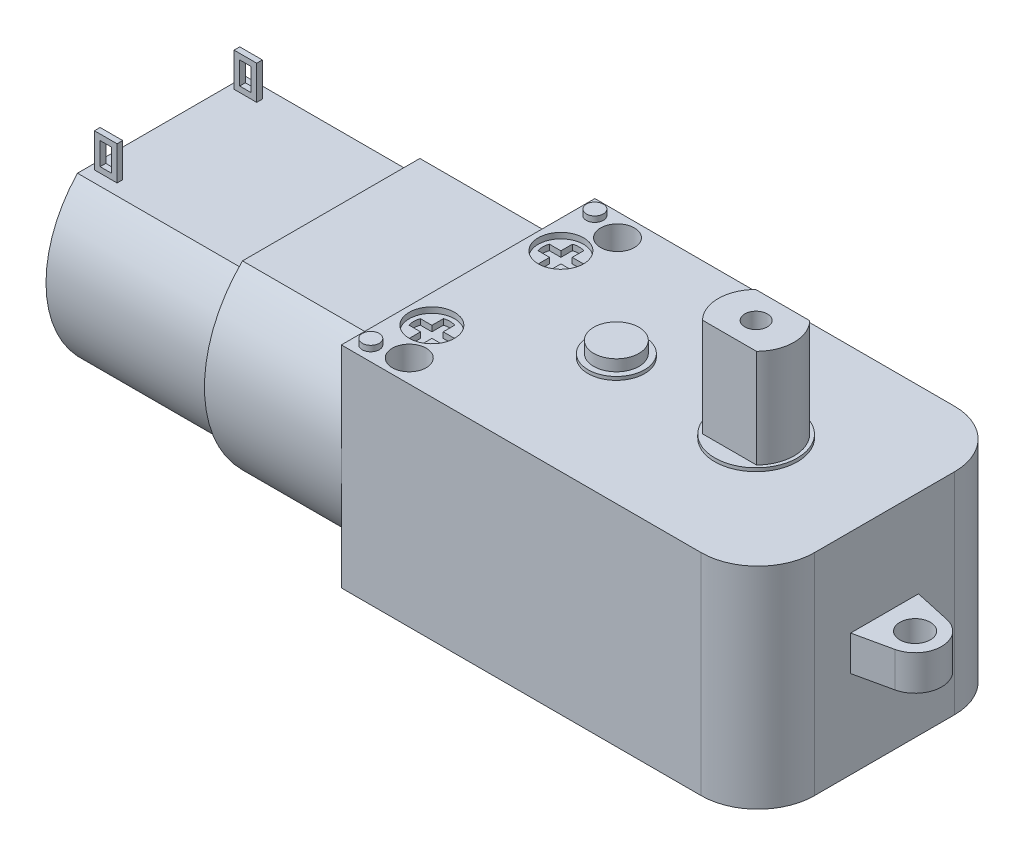
SolidWorks part; units mm, degrees
ref_plane "Front Plane" through (0, 0, 0) normal (0, 0, 1) x (1, 0, 0)
ref_plane "Top Plane" through (0, 0, 0) normal (0, 1, 0) x (1, 0, 0)
ref_plane "Right Plane" through (0, 0, 0) normal (1, 0, 0) x (0, 0, -1)
sketch "Sketch1" plane through (0, 0, 0) normal (0, 1, 0) x (1, 0, 0)
  line L1 (0, 0) -> (36.8, 0)
  line L2 (0, 0) -> (0, 22.4)
  line L3 (0, 22.4) -> (36.8, 22.4)
  line L4 (36.8, 0) -> (36.8, 22.4)
  dimension "D1" = 36.8
  dimension "D2" = 22.4
extrude "Extrude1" add sketch "Sketch1" along normal mid plane 18.6
fillet "Fillet1" radius 5 2 edges at (36.8, 0, -22.4) (36.8, 0, 0)
sketch "Sketch2" plane through (0, 0, 0) normal (0, 1, 0) x (1, 0, 0)
  line L0 (36.8, 11.2) -> (43.7927, 11.2) construction
  line L1 (36.8, 5) -> (36.8, 17.4) construction
  line L2 (36.8, 14.2) -> (40.0048, 13.4951)
  line L3 (36.8, 8.2) -> (40.0048, 8.9049)
  line L4 (36.8, 14.2) -> (36.8, 8.2)
  circle A0 centre (39.5, 11.2) radius 1.35
  arc A1 (40.0048, 8.9049) -> (40.0048, 13.4951) centre (39.5, 11.2) ccw
  dimension "D1" = 2.7
  dimension "D3" = 1
  dimension "D2" = 3
  dimension "D4" = 2.7
extrude "Extrude2" add sketch "Sketch2" along normal mid plane 3.1
sketch "Sketch3" plane through (0, 9.3, 0) normal (0, 1, 0) x (1, 0, 0)
  line L0 (36.8, 11.2) -> (0, 11.2) construction
  line L1 (36.8, 5) -> (36.8, 17.4) construction
  line L2 (0, 22.4) -> (0, 0) construction
  circle A0 centre (25.45, 11.2) radius 3.65
  circle A1 centre (13.1, 11.2) radius 2.5
  dimension "D1" = 7.3
  dimension "D2" = 11.35
  dimension "D3" = 5
  dimension "D4" = 12.35
extrude "Extrude3" add sketch "Sketch3" along normal blind 0.3
sketch "Sketch4" plane through (0, 9.6, 0) normal (0, 1, 0) x (1, 0, 0)
  line L0 (22.1, 11.2) -> (28.8, 11.2) construction
  line L1 (23.0625, 8.85) -> (27.8375, 8.85)
  line L2 (23.0625, 13.55) -> (27.8375, 13.55)
  line L3 (22.1, 13.55) -> (28.8, 13.55) construction
  line L4 (22.1, 8.85) -> (28.8, 8.85) construction
  arc A0 (23.0625, 13.55) -> (23.0625, 8.85) centre (25.45, 11.2) ccw
  circle A1 centre (25.45, 11.2) radius 1
  arc A2 (27.8375, 8.85) -> (27.8375, 13.55) centre (25.45, 11.2) ccw
  dimension "D1" = 6.7
  dimension "D2" = 2
  dimension "D3" = 2.35
  dimension "D4" = 2.35
extrude "Extrude4" add sketch "Sketch4" along normal blind 8.7
sketch "Sketch6" plane through (0, 9.6, 0) normal (0, 1, 0) x (1, 0, 0)
  circle A0 centre (13.1, 11.2) radius 2
  dimension "D1" = 4
extrude "Extrude5" add sketch "Sketch6" along normal blind 1
sketch "Sketch7" plane through (0, 9.3, 0) normal (0, 1, 0) x (1, 0, 0)
  line L0 (4, 22.4) -> (4, 0) construction
  line L1 (31.8, 22.4) -> (0, 22.4) construction
  line L2 (0, 0) -> (31.8, 0) construction
  line L3 (0, 22.4) -> (0, 0) construction
  circle A0 centre (4, 20.4) radius 1.5
  circle A1 centre (4, 2) radius 1.5
  dimension "D1" = 3
  dimension "D2" = 2
  dimension "D3" = 2
  dimension "D4" = 4
extrude "Extrude6" cut sketch "Sketch7" against normal through all
sketch "Sketch8" plane through (0, 9.3, 0) normal (0, 1, 0) x (1, 0, 0)
  line L0 (2.5, 22.4) -> (2.5, 0) construction
  line L1 (31.8, 22.4) -> (0, 22.4) construction
  line L2 (0, 0) -> (31.8, 0) construction
  line L3 (0, 22.4) -> (0, 0) construction
  circle A0 centre (2.5, 16.9) radius 2
  circle A1 centre (2.5, 5.5) radius 2
  dimension "D1" = 4
  dimension "D2" = 5.5
  dimension "D3" = 5.5
  dimension "D4" = 2.5
extrude "Extrude7" cut sketch "Sketch8" against normal blind 0.5
sketch "Sketch9" plane through (0, 8.8, 0) normal (0, 1, 0) x (1, 0, 0)
  line L0 (2.5, 18.5) -> (2.5, 15.3) construction
  line L1 (4.1, 16.9) -> (0.9, 16.9) construction
  line L2 (0.9, 5.5) -> (4.1, 5.5) construction
  line L3 (2.5, 7.1) -> (2.5, 3.9) construction
  line L4 (2, 7.0199) -> (2, 6)
  line L5 (3, 7.0199) -> (3, 6)
  line L6 (4.0199, 17.4) -> (3, 17.4)
  line L7 (2, 18.4199) -> (2, 17.4)
  line L8 (0.9801, 5) -> (2, 5)
  line L9 (4.0199, 16.4) -> (3, 16.4)
  line L10 (3, 18.4199) -> (3, 17.4)
  line L11 (0.9801, 6) -> (2, 6)
  line L12 (2, 18.5) -> (2, 15.3) construction
  line L13 (3, 18.5) -> (3, 15.3) construction
  line L14 (4.1, 17.4) -> (0.9, 17.4) construction
  line L15 (4.1, 16.4) -> (0.9, 16.4) construction
  line L16 (2, 7.1) -> (2, 3.9) construction
  line L17 (3, 7.1) -> (3, 3.9) construction
  line L18 (0.9, 6) -> (4.1, 6) construction
  line L19 (0.9, 5) -> (4.1, 5) construction
  line L20 (2, 17.4) -> (0.9801, 17.4)
  line L21 (2, 16.4) -> (2, 15.3801)
  line L22 (3, 16.4) -> (3, 15.3801)
  line L23 (2, 16.4) -> (0.9801, 16.4)
  line L24 (3, 6) -> (4.0199, 6)
  line L25 (2, 5) -> (2, 3.9801)
  line L26 (3, 5) -> (3, 3.9801)
  line L27 (3, 5) -> (4.0199, 5)
  arc A0 (3, 7.0199) -> (2, 7.0199) centre (2.5, 5.5) ccw
  arc A1 (3, 18.4199) -> (2, 18.4199) centre (2.5, 16.9) ccw
  arc A2 (4.0199, 16.4) -> (4.0199, 17.4) centre (2.5, 16.9) ccw
  arc A3 (2, 15.3801) -> (3, 15.3801) centre (2.5, 16.9) ccw
  arc A4 (0.9801, 17.4) -> (0.9801, 16.4) centre (2.5, 16.9) ccw
  arc A5 (4.0199, 5) -> (4.0199, 6) centre (2.5, 5.5) ccw
  arc A6 (2, 3.9801) -> (3, 3.9801) centre (2.5, 5.5) ccw
  arc A7 (0.9801, 6) -> (0.9801, 5) centre (2.5, 5.5) ccw
  dimension "D1" = 3.2
  dimension "D6" = 1.6
  dimension "D2" = 0.5
  dimension "D3" = 0.5
  dimension "D4" = 0.5
  dimension "D5" = 0.5
extrude "Extrude8" cut sketch "Sketch9" against normal blind 0.5
sketch "Sketch10" plane through (0, 9.3, 0) normal (0, 1, 0) x (1, 0, 0)
  line L0 (1.3, 22.4) -> (1.3, 0) construction
  line L1 (31.8, 22.4) -> (0, 22.4) construction
  line L2 (0, 0) -> (31.8, 0) construction
  line L3 (0, 22.4) -> (0, 0) construction
  circle A0 centre (1.3, 21.1) radius 0.75
  circle A1 centre (1.3, 1.3) radius 0.75
  dimension "D1" = 1.5
  dimension "D3" = 1.3
  dimension "D4" = 1.3
  dimension "D2" = 1.3
extrude "Extrude9" add sketch "Sketch10" along normal blind 0.5
sketch "Sketch12" plane through (0, 0, 0) normal (-1, 0, 0) x (0, 0, 1)
  line L0 (-22.4, 9.3) -> (0, -9.3) construction
  line L1 (-19.0384, 8) -> (-3.3616, 8)
  line L4 (-3.3616, -8) -> (-19.0384, -8)
  line L5 (-11.2, 0) -> (-22.4, 0) construction
  arc A0 (-19.0384, 8) -> (-19.0384, -8) centre (-11.2, 0) ccw
  arc A1 (-3.3616, -8) -> (-3.3616, 8) centre (-11.2, 0) ccw
  dimension "D1" = 16
  dimension "D2" = 8
extrude "Extrude11" add sketch "Sketch12" along normal blind 12.1
sketch "Sketch13" plane through (-12.1, 0, 0) normal (-1, 0, 0) x (0, 0, 1)
  line L14 (-18.6189, -7) -> (-3.7811, -7)
  line L15 (-3.7811, 7) -> (-18.6189, 7)
  line L16 (-18.6189, -7) -> (-3.7811, -7)
  line L17 (-3.7811, 7) -> (-18.6189, 7)
  arc A14 (-18.6189, 7) -> (-18.6189, -7) centre (-11.2, 0) ccw
  arc A15 (-3.7811, -7) -> (-3.7811, 7) centre (-11.2, 0) ccw
  arc A16 (-18.6189, 7) -> (-18.6189, -7) centre (-11.2, 0) ccw
  arc A17 (-3.7811, -7) -> (-3.7811, 7) centre (-11.2, 0) ccw
  dimension "D3" = 1
extrude "Extrude12" add sketch "Sketch13" along normal blind 15
sketch "Sketch14" plane through (-27.1, 0, 0) normal (-1, 0, 0) x (0, 0, 1)
  line L0 (-18.6189, -7) -> (-3.7811, 7) construction
  circle A0 centre (-11.2, 0) radius 4
  dimension "D1" = 8
extrude "Extrude13" add sketch "Sketch14" along normal blind 1
sketch "Sketch15" plane through (-28.1, 0, 0) normal (-1, 0, 0) x (0, 0, 1)
  circle A0 centre (-11.2, 0) radius 1
  dimension "D1" = 2
extrude "Extrude14" add sketch "Sketch15" along normal blind 1
sketch "Sketch16" plane through (0, 7, 0) normal (0, 1, 0) x (1, 0, 0)
  line L0 (-27.1, 18.6189) -> (-12.1, 18.6189) construction
  line L1 (-26.6, 17.6189) -> (-24.6, 17.6189)
  line L2 (-26.6, 17.6189) -> (-26.6, 17.1189)
  line L3 (-26.6, 17.1189) -> (-24.6, 17.1189)
  line L4 (-24.6, 17.6189) -> (-24.6, 17.1189)
  line L5 (-26.6, 5.2811) -> (-24.6, 5.2811)
  line L6 (-26.6, 5.2811) -> (-26.6, 4.7811)
  line L7 (-26.6, 4.7811) -> (-24.6, 4.7811)
  line L8 (-24.6, 5.2811) -> (-24.6, 4.7811)
  line L9 (-27.1, 3.7811) -> (-12.1, 3.7811) construction
  line L10 (-27.1, 3.7811) -> (-27.1, 18.6189) construction
  dimension "D1" = 2
  dimension "D2" = 0.5
  dimension "D3" = 0.5
  dimension "D4" = 2
  dimension "D5" = 1
  dimension "D6" = 1
  dimension "D7" = 0.5
  dimension "D8" = 0.5
extrude "Extrude15" add sketch "Sketch16" along normal blind 3
sketch "Sketch17" plane through (0, 0, -4.7811) normal (0, 0, 1) x (1, 0, 0)
  line L0 (-26.6, 10) -> (-24.6, 10) construction
  line L1 (-26.1, 9.5) -> (-25.1, 9.5)
  line L2 (-26.1, 9.5) -> (-26.1, 7.5)
  line L3 (-26.1, 7.5) -> (-25.1, 7.5)
  line L4 (-25.1, 9.5) -> (-25.1, 7.5)
  line L5 (-26.6, 7) -> (-24.6, 7) construction
  line L6 (-26.6, 10) -> (-26.6, 7) construction
  line L7 (-24.6, 10) -> (-24.6, 7) construction
  dimension "D1" = 0.5
  dimension "D2" = 0.5
  dimension "D3" = 0.5
  dimension "D4" = 0.5
extrude "Extrude16" cut sketch "Sketch17" against normal through all
